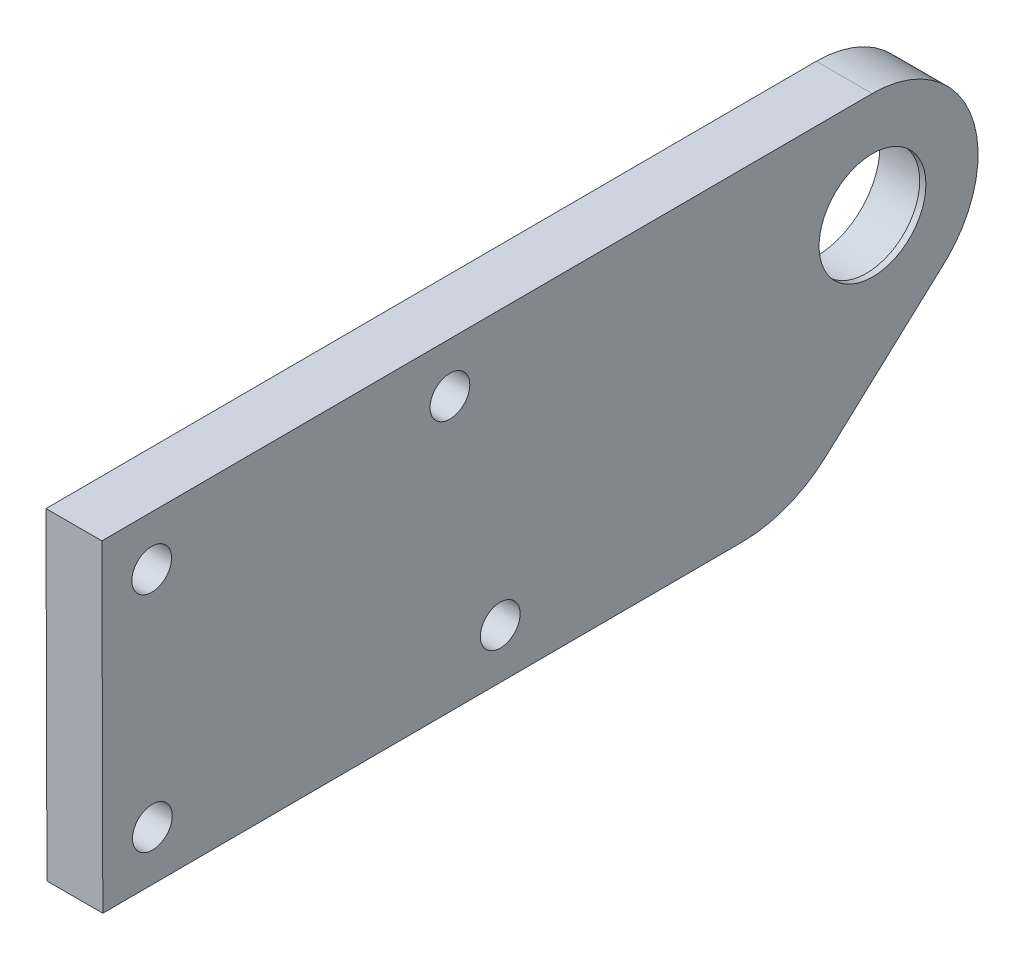
SolidWorks part; units mm, degrees
ref_plane "前视基准面" through (0, 0, 0) normal (0, 0, 1) x (1, 0, 0)
ref_plane "上视基准面" through (0, 0, 0) normal (0, 1, 0) x (1, 0, 0)
ref_plane "右视基准面" through (0, 0, 0) normal (1, 0, 0) x (0, 0, -1)
sketch "草图1" plane through (0, 0, 0) normal (1, 0, 0) x (0, 0, -1)
  line L47 (-61.9107, -17.7849) -> (-10.4109, -17.6369)
  line L48 (-3.6943, -15.0194) -> (6.0537, -6.1126)
  line L49 (-61.9854, 8.215) -> (-61.9107, -17.7849)
  line L50 (-61.9854, 8.215) -> (0.0144, 8.3932)
  circle A0 centre (0.0388, -0.1068) radius 4.3
  circle A166 centre (-57.9739, 4.2265) radius 1.6
  arc A169 (6.0537, -6.1126) -> (0.0144, 8.3932) centre (0.0388, -0.1068) ccw
  circle A170 centre (-29.9223, -13.6929) radius 1.6
  circle A171 centre (-33.974, 4.2955) radius 1.6
  circle A175 centre (-57.9222, -13.7734) radius 1.6
  arc A176 (-10.4109, -17.6369) -> (-3.6943, -15.0194) centre (-10.4396, -7.6369) ccw
  point P0 (-150, 0)
  point P1 (135, 0)
  point P9 (-344.9533, 138.7825)
  point P10 (187.1329, 101.1747)
  point P11 (165.9429, -19)
  point P12 (-156.9154, -19)
  dimension "D7" = 4
  dimension "D8" = 22
  dimension "D10" = 8.5
  dimension "D4" = 4
  dimension "D11" = 62
  dimension "D13" = 26
  dimension "D14" = 8.6
  dimension "D6" = 28
  dimension "D5" = 4
  dimension "D2" = 18
  dimension "D1" = 24
  dimension "D3" = 4
extrude "凸台-拉伸1" add sketch "草图1" along normal blind 4.5
sketch "草图2" plane through (0, 0, 0) normal (1, 0, 0) x (0, 0, -1)
  circle A0 centre (0.0388, -0.1068) radius 5.1
  dimension "D1" = 10.2
extrude "切除-拉伸1" cut sketch "草图2" along normal blind 4
